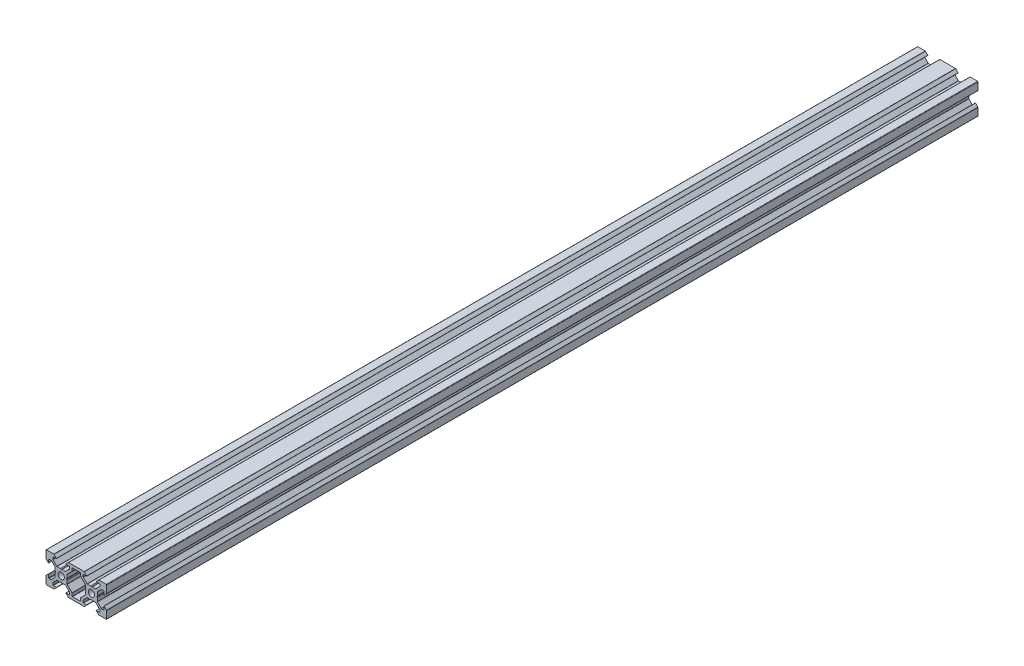
SolidWorks part; units mm, degrees
material "6063-T5"
ref_plane "Plan de face" through (0, 0, 0) normal (0, 0, 1) x (1, 0, 0)
ref_plane "Plan de dessus" through (0, 0, 0) normal (0, 1, 0) x (1, 0, 0)
ref_plane "Plan de droite" through (0, 0, 0) normal (1, 0, 0) x (0, 0, -1)
sketch "Esquisse1" plane through (0, 0, 0) normal (0, 0, 1) x (1, 0, 0)
  line L0 (12.1877, 2.7347) -> (11.6681, 3.0347)
  line L1 (11.6681, 3.0347) -> (9.472, 3.0347)
  line L2 (9.2599, 3.1225) -> (6.7763, 5.6062)
  line L3 (6.6884, 5.8183) -> (6.6884, 7.034)
  line L4 (6.9884, 7.334) -> (8.9877, 7.334)
  line L5 (9.0585, 7.5047) -> (7.517, 9.0462)
  line L6 (7.3049, 9.134) -> (2.1877, 9.134)
  line L7 (2.1877, 9.134) -> (-2.9294, 9.134)
  line L8 (-3.1415, 9.0462) -> (-4.683, 7.5047)
  line L9 (-4.6123, 7.334) -> (-2.6129, 7.334)
  line L10 (-2.3129, 7.034) -> (-2.3129, 5.8183)
  line L11 (-2.4008, 5.6062) -> (-4.8844, 3.1225)
  line L12 (-5.0965, 3.0347) -> (-7.2926, 3.0347)
  line L13 (-7.2926, 3.0347) -> (-7.8123, 2.7347)
  line L14 (-7.8123, 2.7347) -> (-8.3319, 3.0347)
  line L15 (-8.3319, 3.0347) -> (-10.528, 3.0347)
  line L16 (-10.7401, 3.1225) -> (-13.2237, 5.6062)
  line L17 (-13.3116, 5.8183) -> (-13.3116, 7.034)
  line L18 (-13.0116, 7.334) -> (-11.0123, 7.334)
  line L19 (-10.9415, 7.5047) -> (-12.483, 9.0462)
  line L20 (-12.6951, 9.134) -> (-17.5123, 9.134)
  line L21 (-17.8123, 8.834) -> (-17.8123, 4.0169)
  line L22 (-17.7244, 3.8047) -> (-16.183, 2.2633)
  line L23 (-16.0123, 2.334) -> (-16.0123, 4.3334)
  line L24 (-15.7123, 4.6334) -> (-14.4965, 4.6334)
  line L25 (-14.2844, 4.5455) -> (-11.8008, 2.0619)
  line L26 (-11.7129, 1.8498) -> (-11.7129, -0.3464)
  line L27 (-11.7129, -0.3464) -> (-11.4129, -0.866)
  line L28 (-11.4129, -0.866) -> (-11.7129, -1.3856)
  line L29 (-11.7129, -1.3856) -> (-11.7129, -3.5817)
  line L30 (-11.8008, -3.7938) -> (-14.2844, -6.2775)
  line L31 (-14.4965, -6.3653) -> (-15.7123, -6.3653)
  line L32 (-16.0123, -6.0653) -> (-16.0123, -4.066)
  line L33 (-16.183, -3.9953) -> (-17.7244, -5.5367)
  line L34 (-17.8123, -5.7488) -> (-17.8123, -10.566)
  line L35 (-17.5123, -10.866) -> (-12.6951, -10.866)
  line L36 (-12.483, -10.7781) -> (-10.9415, -9.2367)
  line L37 (-11.0123, -9.066) -> (-13.0116, -9.066)
  line L38 (-13.3116, -8.766) -> (-13.3116, -7.5502)
  line L39 (-13.2237, -7.3381) -> (-10.7401, -4.8545)
  line L40 (-10.528, -4.7666) -> (-8.3319, -4.7666)
  line L41 (-8.3319, -4.7666) -> (-7.8123, -4.4666)
  line L42 (-7.8123, -4.4666) -> (-7.2926, -4.7666)
  line L43 (-7.2926, -4.7666) -> (-5.0965, -4.7666)
  line L44 (-4.8844, -4.8545) -> (-2.4008, -7.3381)
  line L45 (-2.3129, -7.5502) -> (-2.3129, -8.766)
  line L46 (-2.6129, -9.066) -> (-4.6123, -9.066)
  line L47 (-4.683, -9.2367) -> (-3.1415, -10.7781)
  line L48 (-2.9294, -10.866) -> (2.1877, -10.866)
  line L49 (2.1877, -10.866) -> (7.3049, -10.866)
  line L50 (7.517, -10.7781) -> (9.0585, -9.2367)
  line L51 (8.9877, -9.066) -> (6.9884, -9.066)
  line L52 (6.6884, -8.766) -> (6.6884, -7.5502)
  line L53 (6.7763, -7.3381) -> (9.2599, -4.8545)
  line L54 (9.472, -4.7666) -> (11.6681, -4.7666)
  line L55 (11.6681, -4.7666) -> (12.1877, -4.4666)
  line L56 (12.1877, -4.4666) -> (12.7074, -4.7666)
  line L57 (12.7074, -4.7666) -> (14.9035, -4.7666)
  line L58 (15.1156, -4.8545) -> (17.5992, -7.3381)
  line L59 (17.6871, -7.5502) -> (17.6871, -8.766)
  line L60 (17.3871, -9.066) -> (15.3877, -9.066)
  line L61 (15.317, -9.2367) -> (16.8585, -10.7781)
  line L62 (17.0706, -10.866) -> (21.8877, -10.866)
  line L63 (22.1877, -10.566) -> (22.1877, -5.7488)
  line L64 (22.0999, -5.5367) -> (20.5585, -3.9953)
  line L65 (20.3877, -4.066) -> (20.3877, -6.0653)
  line L66 (20.0877, -6.3653) -> (18.872, -6.3653)
  line L67 (18.6599, -6.2775) -> (16.1763, -3.7938)
  line L68 (16.0884, -3.5817) -> (16.0884, -1.3856)
  line L69 (16.0884, -1.3856) -> (15.7884, -0.866)
  line L70 (15.7884, -0.866) -> (16.0884, -0.3464)
  line L71 (16.0884, -0.3464) -> (16.0884, 1.8498)
  line L72 (16.1763, 2.0619) -> (18.6599, 4.5455)
  line L73 (18.872, 4.6334) -> (20.0877, 4.6334)
  line L74 (20.3877, 4.3334) -> (20.3877, 2.334)
  line L75 (20.5585, 2.2633) -> (22.0999, 3.8047)
  line L76 (22.1877, 4.0169) -> (22.1877, 8.834)
  line L77 (21.8877, 9.134) -> (17.0706, 9.134)
  line L78 (16.8585, 9.0462) -> (15.317, 7.5047)
  line L79 (15.3877, 7.334) -> (17.3871, 7.334)
  line L80 (17.6871, 7.034) -> (17.6871, 5.8183)
  line L81 (17.5992, 5.6062) -> (15.1156, 3.1225)
  line L82 (14.9035, 3.0347) -> (12.7074, 3.0347)
  line L83 (12.7074, 3.0347) -> (12.1877, 2.7347)
  line L180 (4.9271, -8.766) -> (4.9271, -7.1902)
  line L181 (5.015, -6.9781) -> (8.1992, -3.7938)
  line L182 (8.2871, -3.5817) -> (8.2871, -1.3856)
  line L183 (8.2871, -1.3856) -> (8.5871, -0.866)
  line L184 (8.5871, -0.866) -> (8.2871, -0.3464)
  line L185 (8.2871, -0.3464) -> (8.2871, 1.8498)
  line L186 (8.1992, 2.0619) -> (5.015, 5.2462)
  line L187 (4.9271, 5.4583) -> (4.9271, 7.034)
  line L188 (4.6271, 7.334) -> (2.1877, 7.334)
  line L189 (2.1877, 7.334) -> (-0.2516, 7.334)
  line L190 (-0.5516, 7.034) -> (-0.5516, 5.4583)
  line L191 (-0.6395, 5.2462) -> (-3.8237, 2.0619)
  line L192 (-3.9116, 1.8498) -> (-3.9116, -0.3464)
  line L193 (-3.9116, -0.3464) -> (-4.2116, -0.866)
  line L194 (-4.2116, -0.866) -> (-3.9116, -1.3856)
  line L195 (-3.9116, -1.3856) -> (-3.9116, -3.5817)
  line L196 (-3.8237, -3.7938) -> (-0.6395, -6.9781)
  line L197 (-0.5516, -7.1902) -> (-0.5516, -8.766)
  line L198 (-0.2516, -9.066) -> (2.1877, -9.066)
  line L199 (2.1877, -9.066) -> (4.6271, -9.066)
  arc A0 (-7.8123, 1.234) -> (-9.9123, -0.866) centre (-7.8123, -0.866) ccw
  arc A1 (-9.9123, -0.866) -> (-7.8123, -2.966) centre (-7.8123, -0.866) ccw
  arc A2 (-7.8123, -2.966) -> (-5.7123, -0.866) centre (-7.8123, -0.866) ccw
  arc A3 (-5.7123, -0.866) -> (-7.8123, 1.234) centre (-7.8123, -0.866) ccw
  arc A4 (12.1877, 1.234) -> (10.0877, -0.866) centre (12.1877, -0.866) ccw
  arc A5 (10.0877, -0.866) -> (12.1877, -2.966) centre (12.1877, -0.866) ccw
  arc A6 (12.1877, -2.966) -> (14.2877, -0.866) centre (12.1877, -0.866) ccw
  arc A7 (14.2877, -0.866) -> (12.1877, 1.234) centre (12.1877, -0.866) ccw
  arc A8 (9.2599, 3.1225) -> (9.472, 3.0347) centre (9.472, 3.3347) ccw
  arc A9 (6.6884, 5.8183) -> (6.7763, 5.6062) centre (6.9884, 5.8183) ccw
  arc A10 (6.9884, 7.334) -> (6.6884, 7.034) centre (6.9884, 7.034) ccw
  arc A11 (8.9877, 7.334) -> (9.0585, 7.5047) centre (8.9877, 7.434) ccw
  arc A12 (7.517, 9.0462) -> (7.3049, 9.134) centre (7.3049, 8.834) ccw
  arc A13 (-2.9294, 9.134) -> (-3.1415, 9.0462) centre (-2.9294, 8.834) ccw
  arc A14 (-4.683, 7.5047) -> (-4.6123, 7.334) centre (-4.6123, 7.434) ccw
  arc A15 (-2.3129, 7.034) -> (-2.6129, 7.334) centre (-2.6129, 7.034) ccw
  arc A16 (-2.4008, 5.6062) -> (-2.3129, 5.8183) centre (-2.6129, 5.8183) ccw
  arc A17 (-5.0965, 3.0347) -> (-4.8844, 3.1225) centre (-5.0965, 3.3347) ccw
  arc A18 (-10.7401, 3.1225) -> (-10.528, 3.0347) centre (-10.528, 3.3347) ccw
  arc A19 (-13.3116, 5.8183) -> (-13.2237, 5.6062) centre (-13.0116, 5.8183) ccw
  arc A20 (-13.0116, 7.334) -> (-13.3116, 7.034) centre (-13.0116, 7.034) ccw
  arc A21 (-11.0123, 7.334) -> (-10.9415, 7.5047) centre (-11.0123, 7.434) ccw
  arc A22 (-12.483, 9.0462) -> (-12.6951, 9.134) centre (-12.6951, 8.834) ccw
  arc A23 (-17.5123, 9.134) -> (-17.8123, 8.834) centre (-17.5123, 8.834) ccw
  arc A24 (-17.8123, 4.0169) -> (-17.7244, 3.8047) centre (-17.5123, 4.0169) ccw
  arc A25 (-16.183, 2.2633) -> (-16.0123, 2.334) centre (-16.1123, 2.334) ccw
  arc A26 (-15.7123, 4.6334) -> (-16.0123, 4.3334) centre (-15.7123, 4.3334) ccw
  arc A27 (-14.2844, 4.5455) -> (-14.4965, 4.6334) centre (-14.4965, 4.3334) ccw
  arc A28 (-11.7129, 1.8498) -> (-11.8008, 2.0619) centre (-12.0129, 1.8498) ccw
  arc A29 (-11.8008, -3.7938) -> (-11.7129, -3.5817) centre (-12.0129, -3.5817) ccw
  arc A30 (-14.4965, -6.3653) -> (-14.2844, -6.2775) centre (-14.4965, -6.0653) ccw
  arc A31 (-16.0123, -6.0653) -> (-15.7123, -6.3653) centre (-15.7123, -6.0653) ccw
  arc A32 (-16.0123, -4.066) -> (-16.183, -3.9953) centre (-16.1123, -4.066) ccw
  arc A33 (-17.7244, -5.5367) -> (-17.8123, -5.7488) centre (-17.5123, -5.7488) ccw
  arc A34 (-17.8123, -10.566) -> (-17.5123, -10.866) centre (-17.5123, -10.566) ccw
  arc A35 (-12.6951, -10.866) -> (-12.483, -10.7781) centre (-12.6951, -10.566) ccw
  arc A36 (-10.9415, -9.2367) -> (-11.0123, -9.066) centre (-11.0123, -9.166) ccw
  arc A37 (-13.3116, -8.766) -> (-13.0116, -9.066) centre (-13.0116, -8.766) ccw
  arc A38 (-13.2237, -7.3381) -> (-13.3116, -7.5502) centre (-13.0116, -7.5502) ccw
  arc A39 (-10.528, -4.7666) -> (-10.7401, -4.8545) centre (-10.528, -5.0666) ccw
  arc A40 (-4.8844, -4.8545) -> (-5.0965, -4.7666) centre (-5.0965, -5.0666) ccw
  arc A41 (-2.3129, -7.5502) -> (-2.4008, -7.3381) centre (-2.6129, -7.5502) ccw
  arc A42 (-2.6129, -9.066) -> (-2.3129, -8.766) centre (-2.6129, -8.766) ccw
  arc A43 (-4.6123, -9.066) -> (-4.683, -9.2367) centre (-4.6123, -9.166) ccw
  arc A44 (-3.1415, -10.7781) -> (-2.9294, -10.866) centre (-2.9294, -10.566) ccw
  arc A45 (7.3049, -10.866) -> (7.517, -10.7781) centre (7.3049, -10.566) ccw
  arc A46 (9.0585, -9.2367) -> (8.9877, -9.066) centre (8.9877, -9.166) ccw
  arc A47 (6.6884, -8.766) -> (6.9884, -9.066) centre (6.9884, -8.766) ccw
  arc A48 (6.7763, -7.3381) -> (6.6884, -7.5502) centre (6.9884, -7.5502) ccw
  arc A49 (9.472, -4.7666) -> (9.2599, -4.8545) centre (9.472, -5.0666) ccw
  arc A50 (15.1156, -4.8545) -> (14.9035, -4.7666) centre (14.9035, -5.0666) ccw
  arc A51 (17.6871, -7.5502) -> (17.5992, -7.3381) centre (17.3871, -7.5502) ccw
  arc A52 (17.3871, -9.066) -> (17.6871, -8.766) centre (17.3871, -8.766) ccw
  arc A53 (15.3877, -9.066) -> (15.317, -9.2367) centre (15.3877, -9.166) ccw
  arc A54 (16.8585, -10.7781) -> (17.0706, -10.866) centre (17.0706, -10.566) ccw
  arc A55 (21.8877, -10.866) -> (22.1877, -10.566) centre (21.8877, -10.566) ccw
  arc A56 (22.1877, -5.7488) -> (22.0999, -5.5367) centre (21.8877, -5.7488) ccw
  arc A57 (20.5585, -3.9953) -> (20.3877, -4.066) centre (20.4877, -4.066) ccw
  arc A58 (20.0877, -6.3653) -> (20.3877, -6.0653) centre (20.0877, -6.0653) ccw
  arc A59 (18.6599, -6.2775) -> (18.872, -6.3653) centre (18.872, -6.0653) ccw
  arc A60 (16.0884, -3.5817) -> (16.1763, -3.7938) centre (16.3884, -3.5817) ccw
  arc A61 (16.1763, 2.0619) -> (16.0884, 1.8498) centre (16.3884, 1.8498) ccw
  arc A62 (18.872, 4.6334) -> (18.6599, 4.5455) centre (18.872, 4.3334) ccw
  arc A63 (20.3877, 4.3334) -> (20.0877, 4.6334) centre (20.0877, 4.3334) ccw
  arc A64 (20.3877, 2.334) -> (20.5585, 2.2633) centre (20.4877, 2.334) ccw
  arc A65 (22.0999, 3.8047) -> (22.1877, 4.0169) centre (21.8877, 4.0169) ccw
  arc A66 (22.1877, 8.834) -> (21.8877, 9.134) centre (21.8877, 8.834) ccw
  arc A67 (17.0706, 9.134) -> (16.8585, 9.0462) centre (17.0706, 8.834) ccw
  arc A68 (15.317, 7.5047) -> (15.3877, 7.334) centre (15.3877, 7.434) ccw
  arc A69 (17.6871, 7.034) -> (17.3871, 7.334) centre (17.3871, 7.034) ccw
  arc A70 (17.5992, 5.6062) -> (17.6871, 5.8183) centre (17.3871, 5.8183) ccw
  arc A71 (14.9035, 3.0347) -> (15.1156, 3.1225) centre (14.9035, 3.3347) ccw
  arc A130 (4.6271, -9.066) -> (4.9271, -8.766) centre (4.6271, -8.766) ccw
  arc A131 (5.015, -6.9781) -> (4.9271, -7.1902) centre (5.2271, -7.1902) ccw
  arc A132 (8.1992, -3.7938) -> (8.2871, -3.5817) centre (7.9871, -3.5817) ccw
  arc A133 (8.2871, 1.8498) -> (8.1992, 2.0619) centre (7.9871, 1.8498) ccw
  arc A134 (4.9271, 5.4583) -> (5.015, 5.2462) centre (5.2271, 5.4583) ccw
  arc A135 (4.9271, 7.034) -> (4.6271, 7.334) centre (4.6271, 7.034) ccw
  arc A136 (-0.2516, 7.334) -> (-0.5516, 7.034) centre (-0.2516, 7.034) ccw
  arc A137 (-0.6395, 5.2462) -> (-0.5516, 5.4583) centre (-0.8516, 5.4583) ccw
  arc A138 (-3.8237, 2.0619) -> (-3.9116, 1.8498) centre (-3.6116, 1.8498) ccw
  arc A139 (-3.9116, -3.5817) -> (-3.8237, -3.7938) centre (-3.6116, -3.5817) ccw
  arc A140 (-0.5516, -7.1902) -> (-0.6395, -6.9781) centre (-0.8516, -7.1902) ccw
  arc A141 (-0.5516, -8.766) -> (-0.2516, -9.066) centre (-0.2516, -8.766) ccw
extrude "Boss.-Extru.2" add sketch "Esquisse1" along normal blind 575
